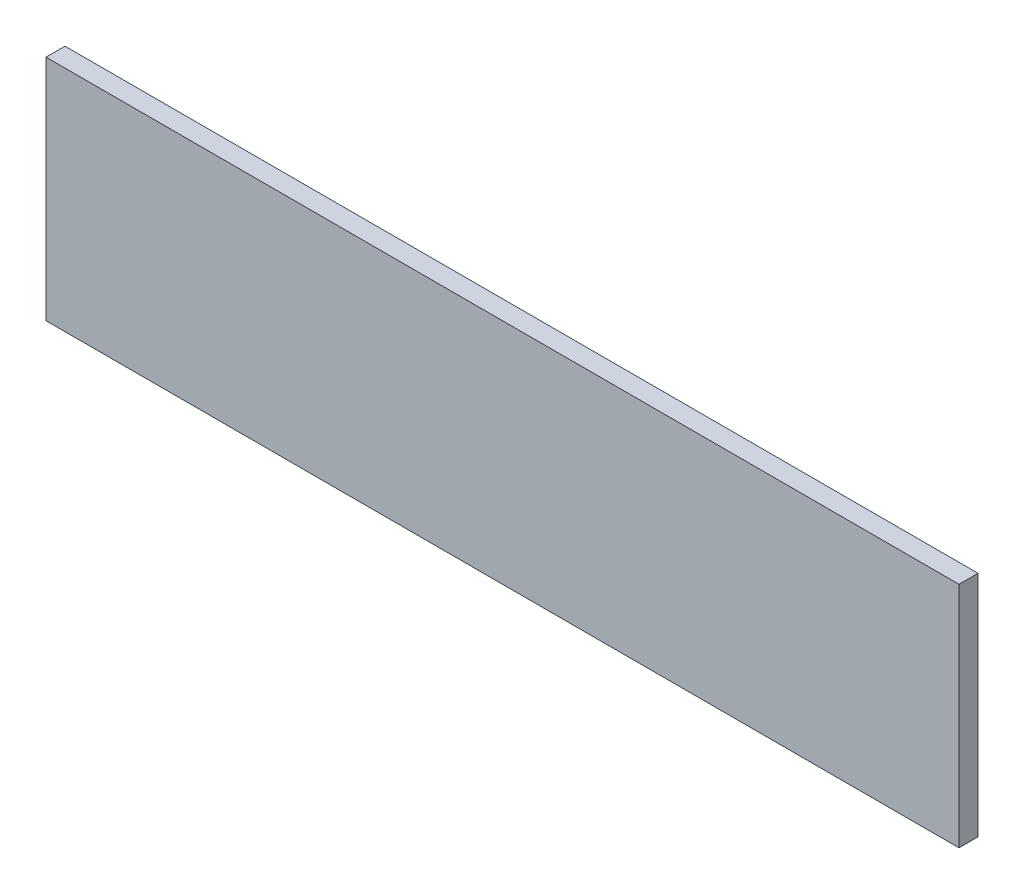
SolidWorks part; units mm, degrees
material "PVC 0.007 Plasticized"
ref_plane "Front Plane" through (0, 0, 0) normal (0, 0, 1) x (1, 0, 0)
ref_plane "Top Plane" through (0, 0, 0) normal (0, 1, 0) x (1, 0, 0)
ref_plane "Right Plane" through (0, 0, 0) normal (1, 0, 0) x (0, 0, -1)
sketch "Sketch1" plane through (0, 0, 0) normal (1, 0, 0) x (0, 0, -1)
  line L1 (-3.175, -38.1) -> (3.175, -38.1)
  line L2 (-3.175, -38.1) -> (-3.175, 38.1)
  line L3 (-3.175, 38.1) -> (3.175, 38.1)
  line L4 (3.175, -38.1) -> (3.175, 38.1)
  line L5 (-3.175, -38.1) -> (3.175, 38.1) construction
  line L6 (-3.175, 38.1) -> (3.175, -38.1) construction
  point P0 (0, 0)
  dimension "D1" = 76.2
  dimension "D2" = 6.35
extrude "Boss-Extrude1" add sketch "Sketch1" along normal blind 304.8
equation "\"D2@Sketch1\"=1in/4"
